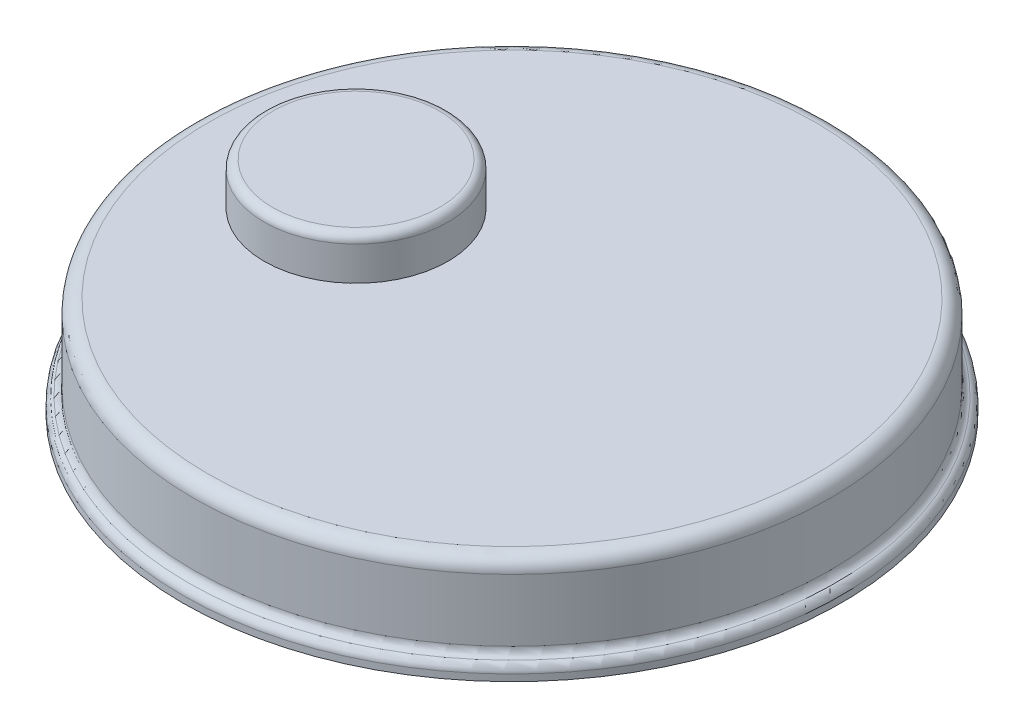
SolidWorks part; units mm, degrees
ref_plane "Front Plane" through (0, 0, 0) normal (0, 0, 1) x (1, 0, 0)
ref_plane "Top Plane" through (0, 0, 0) normal (0, 1, 0) x (1, 0, 0)
ref_plane "Right Plane" through (0, 0, 0) normal (1, 0, 0) x (0, 0, -1)
sketch "Sketch1" plane through (0, 0, 0) normal (0, 0, 1) x (1, 0, 0)
  line L0 (-20.4911, 41.4397) -> (92.0089, 41.4397)
  line L1 (92.0089, 41.4397) -> (92.0089, 11.4397)
  line L2 (92.0089, 11.4397) -> (96.0089, 11.4397)
  line L3 (96.0089, 11.4397) -> (96.0089, 6.4397)
  line L4 (96.0089, 6.4397) -> (-20.4911, 6.4397)
  line L5 (-20.4911, 6.4397) -> (-20.4911, 41.4397) construction
  line L6 (-20.4911, 41.4397) -> (-20.4911, 6.4397)
  dimension "D1" = 112.5
  dimension "D2" = 30
  dimension "D3" = 5
  dimension "D4" = 4
revolve "Revolve1" add sketch "Sketch1" angle 360 about L5
fillet "Fillet2" radius 3 1 edges at (-20.4911, 11.4397, -112.5)
fillet "Fillet3" radius 3 1 edges at (-20.4911, 11.4397, -116.5)
fillet "Fillet4" radius 5 1 edges at (-20.4911, 41.4397, -112.5)
sketch "Sketch4" plane through (0, 41.4397, 0) normal (0, 1, 0) x (1, 0, 0)
  circle A0 centre (-75.608, 0) radius 32.5
  dimension "D1" = 65
extrude "Boss-Extrude3" add sketch "Sketch4" along normal blind 15
fillet "Fillet6" radius 3 1 edges at (-75.608, 56.4397, 32.5)
sketch "Sketch5" plane through (0, 0, 0) normal (0, 0, 1) x (1, 0, 0)
  line L1 (-46.108, 56.4397) -> (-105.108, 56.4397) construction
  line L2 (-75.608, 506.4397) -> (-75.608, 56.4397)
  dimension "D1" = 450
sketch "Sketch6" plane through (0, 56.4397, 0) normal (0, 1, 0) x (1, 0, 0)
  circle A0 centre (-75.608, 0) radius 22.5
  dimension "D1" = 45
